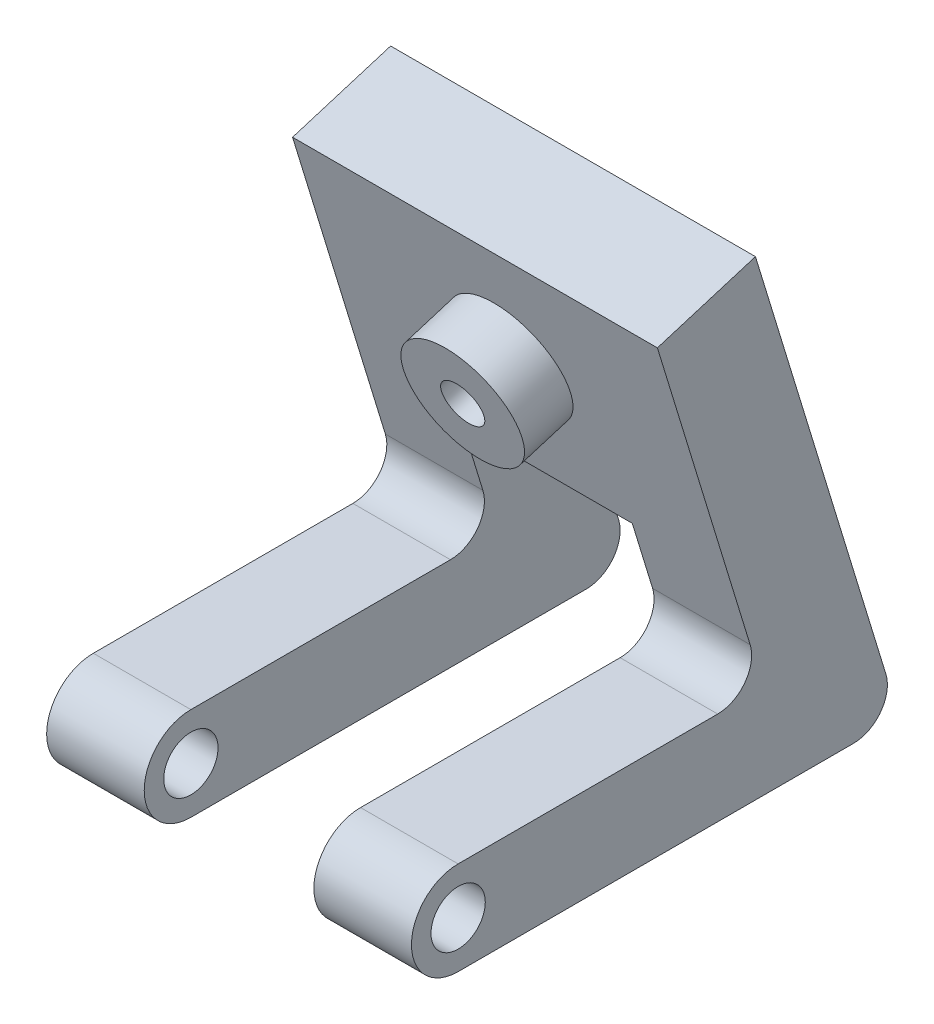
SolidWorks part; units mm, degrees
ref_plane "Front Plane" through (0, 0, 0) normal (0, 0, 1) x (1, 0, 0)
ref_plane "Top Plane" through (0, 0, 0) normal (0, 1, 0) x (1, 0, 0)
ref_plane "Right Plane" through (0, 0, 0) normal (1, 0, 0) x (0, 0, -1)
sketch "Sketch1" plane through (0, 0, 0) normal (1, 0, 0) x (0, 0, -1)
  line L5 (0, 0) -> (-25.4, 0) construction
  line L6 (-4.2676, 14.0808) -> (-35.8448, 4.4267) construction
  line L7 (-35.8448, 4.4267) -> (-33.2373, 4.4267) construction
  line L8 (-25.4, 0) -> (-25.4, 7.62) construction
  line L9 (-4.2676, 14.0808) -> (13.95, 19.6505) construction
  line L10 (0, 3.4925) -> (22.86, 3.4925)
  line L11 (0, -3.4925) -> (33.02, -3.4925)
  line L12 (22.86, 3.4925) -> (14.9134, 29.4846)
  line L13 (33.02, -3.4925) -> (22.252, 31.7282)
  line L14 (22.252, 31.7282) -> (14.9134, 29.4846)
  circle A2 centre (0, 0) radius 2.032
  arc A3 (0, 3.4925) -> (0, -3.4925) centre (0, 0) ccw
  point P14 (0, 0)
  point P19 (0, 0)
  dimension "D1" = 25.4
  dimension "D2" = 17
  dimension "D7" = 4.064
  dimension "D8" = 6.985
  dimension "D3" = 10.922
  dimension "D4" = 33.02
  dimension "D5" = 7.62
  dimension "D6" = 19.05
  dimension "D9" = 22.86
  dimension "D10" = 33.02
  dimension "D11" = 36.83
extrude "Boss-Extrude1" add sketch "Sketch1" along normal blind 27.305
fillet "Fillet1" radius 2.54 2 edges at (13.6525, 3.4925, -22.86) (13.6525, -3.4925, -33.02)
sketch "Sketch2" plane through (0, 0, 0) normal (0, 0, 1) x (1, 0, 0)
  line L0 (0, 18.1299) -> (27.305, 18.1299) construction
  line L1 (0, 29.4846) -> (0, 6.7751) construction
  line L2 (27.305, 29.4846) -> (27.305, 6.7751) construction
  line L3 (13.6525, 11.7475) -> (13.6525, -3.4925) construction
  line L4 (7.3025, 11.7475) -> (20.0025, 11.7475)
  line L5 (7.3025, 11.7475) -> (7.3025, -3.4925)
  line L6 (7.3025, -3.4925) -> (20.0025, -3.4925)
  line L7 (20.0025, 11.7475) -> (20.0025, -3.4925)
  line L9 (27.305, -3.4925) -> (0, -3.4925) construction
  point P13 (0, 0)
  dimension "D1" = 12.7
  dimension "D2" = 7.3025
  dimension "D3" = 15.24
extrude "Cut-Extrude1" cut sketch "Sketch2" against normal through all both and the other way through all
sketch "Sketch3" plane through (0, 6.6901, -21.8824) normal (0, -0.2924, 0.9563) x (1, 0, 0)
  line L0 (13.6525, 5.2885) -> (13.6525, 23.836) construction
  line L1 (7.3025, 5.2885) -> (20.0025, 5.2885) construction
  line L2 (27.305, 23.836) -> (0, 23.836) construction
  line L3 (0, 5.2885) -> (27.305, 5.2885) construction
  line L4 (0, -12.994) -> (0, 23.836) construction
  line L5 (27.305, 23.836) -> (27.305, 0.0889) construction
  line L6 (0, 5.2885) -> (0, 23.836) construction
  line L7 (0, 14.5622) -> (27.305, 14.5622) construction
  circle A0 centre (13.6525, 14.5622) radius 4.445
  circle A1 centre (13.6525, 14.5622) radius 1.5875
  dimension "D1" = 8.89
  dimension "D2" = 3.175
extrude "Boss-Extrude2" add sketch "Sketch3" along normal up to vertex (3.7965 mm away) up to point (0, 19.6505, -13.95)
